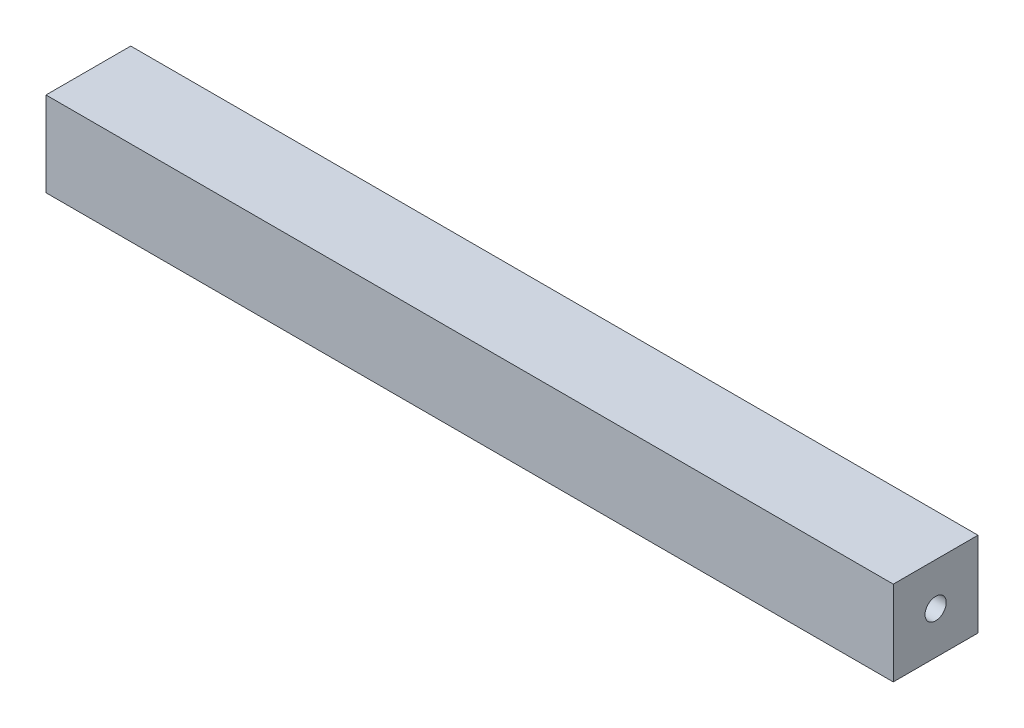
SolidWorks part; units mm, degrees
material "6061-T6 (SS)"
ref_plane "Front Plane" through (0, 0, 0) normal (0, 0, 1) x (1, 0, 0)
ref_plane "Top Plane" through (0, 0, 0) normal (0, 1, 0) x (1, 0, 0)
ref_plane "Right Plane" through (0, 0, 0) normal (1, 0, 0) x (0, 0, -1)
sketch "Sketch1" plane through (0, 0, 0) normal (1, 0, 0) x (0, 0, -1)
  line L1 (12.7, 12.7) -> (-12.7, 12.7)
  line L2 (12.7, 12.7) -> (12.7, -12.7)
  line L3 (12.7, -12.7) -> (-12.7, -12.7)
  line L4 (-12.7, 12.7) -> (-12.7, -12.7)
  line L5 (12.7, 12.7) -> (-12.7, -12.7) construction
  line L6 (12.7, -12.7) -> (-12.7, 12.7) construction
  circle A0 centre (0, 0) radius 3.175
  point P0 (0, 0)
  dimension "D3" = 6.35
  dimension "D1" = 25.4
  dimension "D2" = 25.4
extrude "Boss-Extrude1" add sketch "Sketch1" along normal mid plane 254
